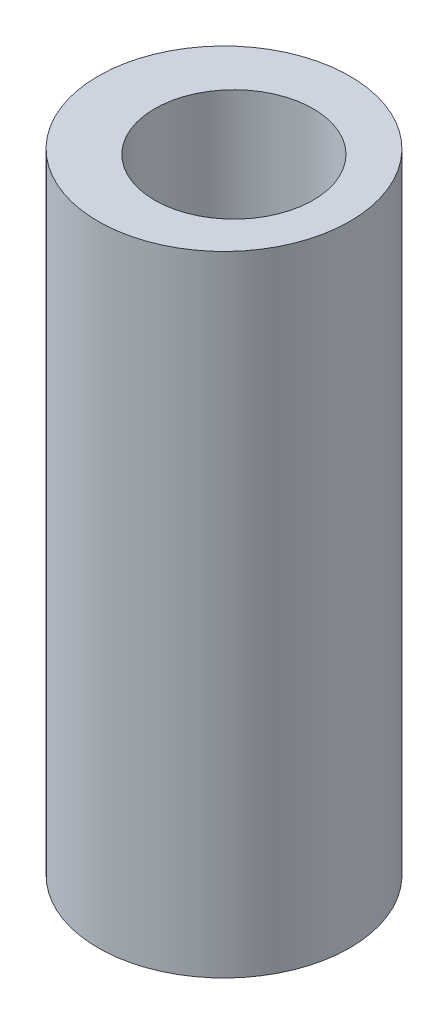
SolidWorks part; units mm, degrees
ref_plane "Front Plane" through (0, 0, 0) normal (0, 0, 1) x (1, 0, 0)
ref_plane "Top Plane" through (0, 0, 0) normal (0, 1, 0) x (1, 0, 0)
ref_plane "Right Plane" through (0, 0, 0) normal (1, 0, 0) x (0, 0, -1)
sketch "Sketch1" plane through (0, 0, 0) normal (0, 0, 1) x (1, 0, 0)
  line L0 (0, 7.564) -> (0, -12.6689) construction
  line L1 (0, 15.875) -> (6.35, 15.875)
  line L2 (0, 15.875) -> (0, -15.875)
  line L3 (0, -15.875) -> (6.35, -15.875)
  line L4 (6.35, 15.875) -> (6.35, -15.875)
  dimension "D1" = 12.7
  dimension "D2" = 31.75
revolve "Revolve1" add sketch "Sketch1" angle 360 about L0
sketch "Sketch2" plane through (0, 0, 0) normal (0, 0, 1) x (1, 0, 0)
  line L0 (4.5, 15.875) -> (4.5, 9.875)
  line L1 (6.35, 15.875) -> (-6.35, 15.875) construction
  line L2 (4.5, 9.875) -> (3.5, 9.875)
  line L3 (3.5, 9.875) -> (3.5, -9.875)
  line L4 (3.5, -9.875) -> (4.5, -9.875)
  line L5 (4.5, -9.875) -> (4.5, -15.875)
  line L6 (4.5, -15.875) -> (0.5, -15.875)
  line L7 (-6.35, -15.875) -> (6.35, -15.875) construction
  line L8 (0.5, -15.875) -> (0.5, 15.875)
  line L9 (0.5, 15.875) -> (4.5, 15.875)
  line L10 (0.5, -7.9823) -> (0.5, -14.4606) construction
  point P13 (4.2566, 9.875)
  point P16 (4.5, 15.875)
  point P17 (4.5, -13.219)
  dimension "D1" = 0.5
  dimension "D2" = 8
  dimension "D3" = 6
  dimension "D4" = 1
revolve "Cut-Revolve3" cut sketch "Sketch2" angle 360 about L10
